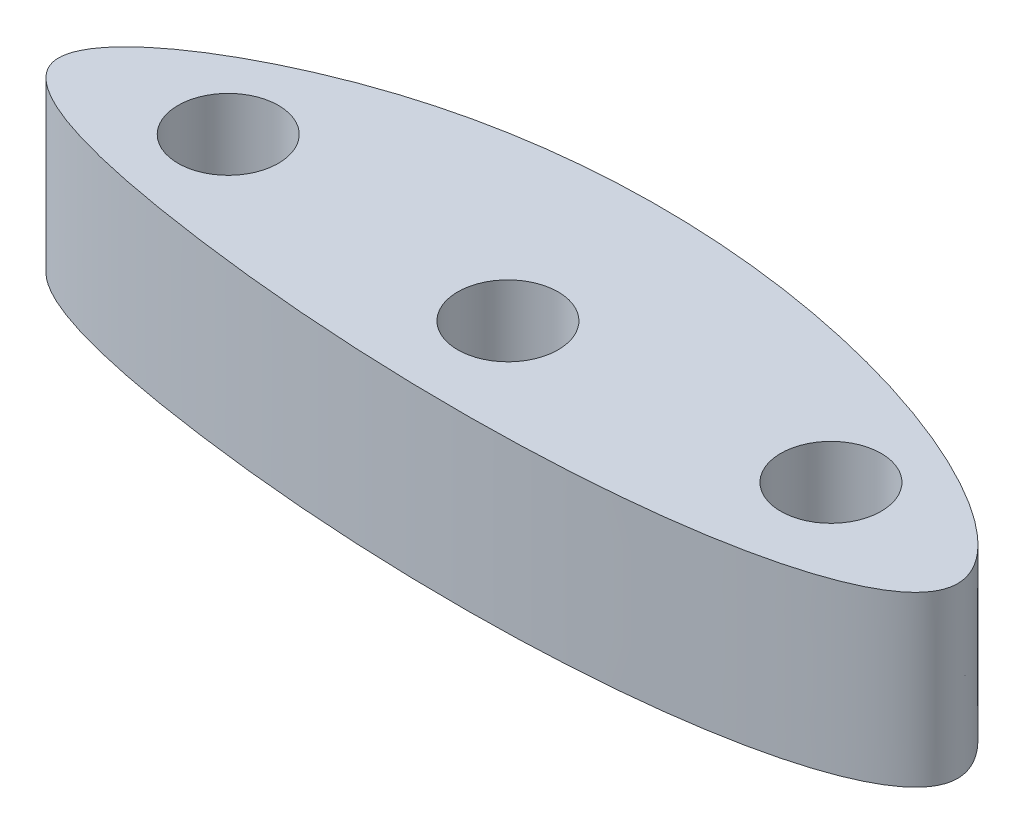
SolidWorks part; units mm, degrees
ref_plane "Front Plane" through (0, 0, 0) normal (0, 0, 1) x (1, 0, 0)
ref_plane "Top Plane" through (0, 0, 0) normal (0, 1, 0) x (1, 0, 0)
ref_plane "Right Plane" through (0, 0, 0) normal (1, 0, 0) x (0, 0, -1)
sketch "Sketch1" plane through (0, 0, 0) normal (0, 1, 0) x (1, 0, 0)
  line L1 (12.2418, 0.1648) -> (12.2418, 8.8543) construction
  circle A1 centre (-2.7582, 1.2427) radius 2.5
  circle A2 centre (12.2418, 0.1648) radius 2.5
  circle A3 centre (27.2418, 1.2427) radius 2.5
  spline S0 degree 3 poles (10.2205, -6.7855) (-15.2644, -0.6301) (9.0458, 14.8561) (53.6021, -2.8236) (10.2205, -6.7855) (-15.2644, -0.6301) (9.0458, 14.8561) knots -0.86636 -0.488517 -0.116417 0 0.13364 0.511483 0.883583 1 1.13364 1.511483 1.883583 only from (-10.2404, 0) to (-10.2404, 0)
  dimension "D1" = 30
  dimension "D2" = 45
  dimension "D3" = 15
extrude "Boss-Extrude1" add sketch "Sketch1" along normal blind 8.4
